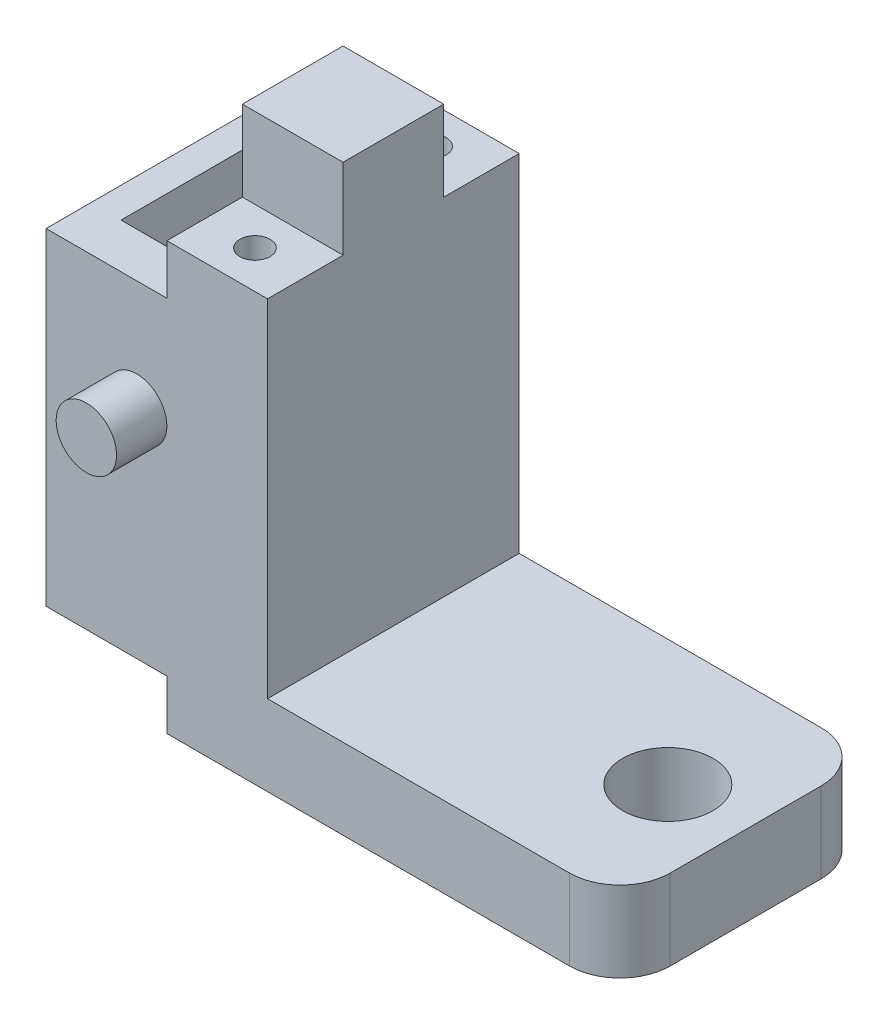
SolidWorks part; units mm, degrees
ref_plane "Front Plane" through (0, 0, 0) normal (0, 0, 1) x (1, 0, 0)
ref_plane "Top Plane" through (0, 0, 0) normal (0, 1, 0) x (1, 0, 0)
ref_plane "Right Plane" through (0, 0, 0) normal (1, 0, 0) x (0, 0, -1)
sketch "Sketch1" plane through (0, 0, 0) normal (0, 1, 0) x (1, 0, 0)
  line L0 (0, 12.5) -> (45, 12.5) construction
  line L1 (0, 0) -> (40, 0)
  line L2 (0, 0) -> (0, 25)
  line L3 (0, 25) -> (40, 25)
  line L4 (45, 5) -> (45, 20)
  circle A1 centre (37.2633, 12.5) radius 4.5
  arc A2 (40, 0) -> (45, 5) centre (40, 5) ccw
  arc A3 (45, 20) -> (40, 25) centre (40, 20) ccw
  point P13 (45, 25)
  dimension "D3" = 9
  dimension "D4" = 7.7367
  dimension "D5" = 5
  dimension "D1" = 25
  dimension "D2" = 45
extrude "Boss-Extrude1" add sketch "Sketch1" along normal blind 8
sketch "Sketch2" plane through (0, 8, 0) normal (0, 1, 0) x (1, 0, 0)
  line L0 (0, 0) -> (40, 0) construction
  line L1 (0, 25) -> (10, 25)
  line L2 (0, 25) -> (0, 0)
  line L3 (0, 0) -> (10, 0)
  line L4 (10, 25) -> (10, 0)
  dimension "D1" = 10
extrude "Boss-Extrude2" add sketch "Sketch2" along normal blind 34.4
sketch "Sketch3" plane through (10, 0, 0) normal (1, 0, 0) x (0, 0, -1)
sketch "Sketch5" plane through (0, 42.4, 0) normal (0, 1, 0) x (1, 0, 0)
  line L6 (10, 25) -> (0, 25) construction
  line L7 (0, 0) -> (10, 0) construction
  line L8 (5, 25) -> (5, 0) construction
  line L12 (0, 25) -> (0, 0) construction
  line L13 (0, 17.5) -> (10, 17.5)
  line L14 (0, 17.5) -> (0, 7.5)
  line L15 (0, 7.5) -> (10, 7.5)
  line L16 (10, 17.5) -> (10, 7.5)
  line L17 (10, 0) -> (10, 25) construction
  dimension "D1" = 10
  dimension "D2" = 10
  dimension "D3" = 7.5
extrude "Boss-Extrude4" add sketch "Sketch5" along normal blind 8
sketch "Sketch6" plane through (0, 42.4, 0) normal (0, 1, 0) x (1, 0, 0)
  circle A0 centre (5, 21.25) radius 1.5
  circle A1 centre (5, 3.75) radius 1.5
  dimension "D1" = 3
  dimension "D2" = 3
extrude "Cut-Extrude1" cut sketch "Sketch6" against normal blind 15
sketch "Sketch10" plane through (0, 0, 0) normal (-1, 0, 0) x (0, 0, 1)
  line L0 (0, 42.4) -> (0, 0) construction
  line L1 (-25, 37.45) -> (0, 37.45)
  line L2 (-25, 37.45) -> (-25, 4.95)
  line L3 (-25, 4.95) -> (0, 4.95)
  line L4 (0, 37.45) -> (0, 4.95)
  line L6 (-25, 0) -> (0, 0) construction
  dimension "D1" = 25
  dimension "D2" = 4.95
  dimension "D3" = 32.5
extrude "Boss-Extrude6" add sketch "Sketch10" along normal blind 12
sketch "Sketch12" plane through (0, 0, -25) normal (0, 0, -1) x (-1, 0, 0)
  line L0 (-10, 42.4) -> (-10, 8) construction
  line L1 (-3, 31.95) -> (9, 31.95)
  line L2 (-3, 31.95) -> (-3, 10.45)
  line L3 (-3, 10.45) -> (9, 10.45)
  line L4 (9, 31.95) -> (9, 10.45)
  line L5 (3, 10.45) -> (3, 31.95) construction
  line L6 (12, 37.45) -> (12, 4.95) construction
  line L9 (12, 37.45) -> (0, 37.45) construction
  line L10 (12, 4.95) -> (0, 4.95) construction
  dimension "D1" = 12
  dimension "D2" = 7
  dimension "D3" = 21.5
  dimension "D4" = 3
  dimension "D5" = 5.5
  dimension "D6" = 5.5
extrude "Cut-Extrude3" cut sketch "Sketch12" against normal blind 21.5
sketch "Sketch13" plane through (0, 0, -25) normal (0, 0, -1) x (-1, 0, 0)
  line L0 (3, 37.45) -> (3, 4.95) construction
  line L1 (12, 37.45) -> (0, 37.45) construction
  line L2 (12, 4.95) -> (0, 4.95) construction
  line L3 (-3, 21.2) -> (9, 21.2) construction
  line L4 (-3, 31.95) -> (-3, 10.45) construction
  line L5 (9, 10.45) -> (9, 31.95) construction
  circle A0 centre (3, 35.2) radius 1
  circle A1 centre (3, 7.2) radius 1
  dimension "D1" = 2
  dimension "D2" = 2
  dimension "D3" = 14
  dimension "D5" = 14
extrude "Cut-Extrude4" cut sketch "Sketch13" against normal blind 10
sketch "Sketch14" plane through (0, 37.45, 0) normal (0, 1, 0) x (1, 0, 0)
  line L0 (0, 0) -> (0, 25) construction
  line L1 (-9, 17.4459) -> (0, 17.4459)
  line L2 (-9, 17.4459) -> (-9, 4.4459)
  line L3 (-9, 4.4459) -> (0, 4.4459)
  line L4 (0, 17.4459) -> (0, 4.4459)
  line L5 (-12, 0) -> (-12, 25) construction
  dimension "D1" = 3
  dimension "D2" = 13
extrude "Cut-Extrude5" cut sketch "Sketch14" against normal through all
sketch "Sketch15" plane through (-12, 0, 0) normal (-1, 0, 0) x (0, 0, 1)
  line L0 (0, 4.95) -> (0, 37.45) construction
  line L1 (-20, 31.45) -> (-5, 31.45)
  line L2 (-20, 31.45) -> (-20, 10.95)
  line L3 (-20, 10.95) -> (-5, 10.95)
  line L4 (-5, 31.45) -> (-5, 10.95)
  line L5 (0, 37.45) -> (-25, 37.45) construction
  line L6 (-25, 4.95) -> (0, 4.95) construction
  line L7 (-25, 37.45) -> (-25, 4.95) construction
  dimension "D1" = 5
  dimension "D2" = 6
  dimension "D3" = 6
  dimension "D4" = 5
extrude "Cut-Extrude6" cut sketch "Sketch15" against normal up to next
sketch "Sketch16" plane through (0, 0, 0) normal (0, 0, 1) x (1, 0, 0)
  circle A0 centre (-3, 26.45) radius 3
  dimension "D1" = 6
extrude "Boss-Extrude7" add sketch "Sketch16" along normal blind 5
